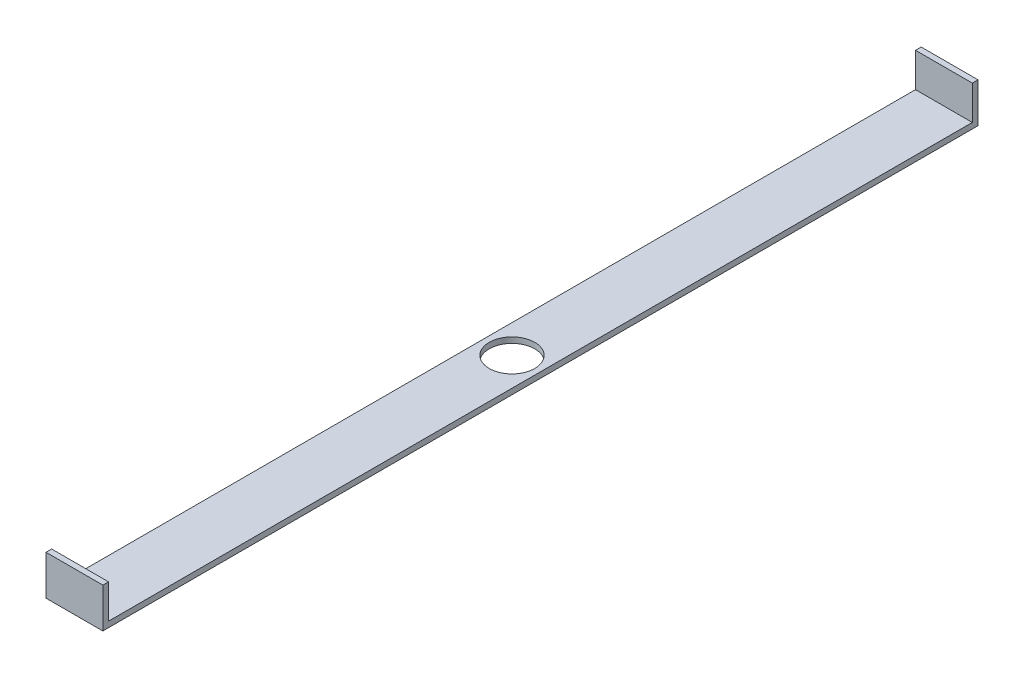
SolidWorks part; units mm, degrees
ref_plane "Front Plane" through (0, 0, 0) normal (0, 0, 1) x (1, 0, 0)
ref_plane "Top Plane" through (0, 0, 0) normal (0, 1, 0) x (1, 0, 0)
ref_plane "Right Plane" through (0, 0, 0) normal (1, 0, 0) x (0, 0, -1)
sketch "Sketch2" plane through (0, 0, 0) normal (0, 0, 1) x (1, 0, 0)
  line L1 (0, 0) -> (50, 0)
  line L2 (0, 0) -> (0, -5)
  line L3 (0, -5) -> (50, -5)
  line L4 (50, 0) -> (50, -5)
  dimension "D1" = 50
  dimension "D2" = 5
extrude "Boss-Extrude1" add sketch "Sketch2" along normal blind 770
sketch "Sketch3" plane through (0, 0, 0) normal (0, 1, 0) x (1, 0, 0)
  line L0 (50, -770) -> (50, 0) construction
  line L1 (0, -770) -> (50, -770)
  line L2 (0, -770) -> (0, -765)
  line L3 (0, -765) -> (50, -765)
  line L4 (50, -770) -> (50, -765)
  line L6 (0, 0) -> (50, 0)
  line L7 (0, 0) -> (0, -5)
  line L8 (0, -5) -> (50, -5)
  line L9 (50, 0) -> (50, -5)
  dimension "D1" = 5
  dimension "D2" = 5
extrude "Boss-Extrude2" add sketch "Sketch3" along normal blind 30
sketch "Sketch4" plane through (0, 0, 0) normal (0, 1, 0) x (1, 0, 0)
  line L0 (25, 0) -> (25, -770) construction
  line L1 (50, 0) -> (0, 0) construction
  line L2 (0, -770) -> (50, -770) construction
  circle A0 centre (25, -385) radius 20
extrude "Cut-Extrude1" cut sketch "Sketch4" against normal blind 30
